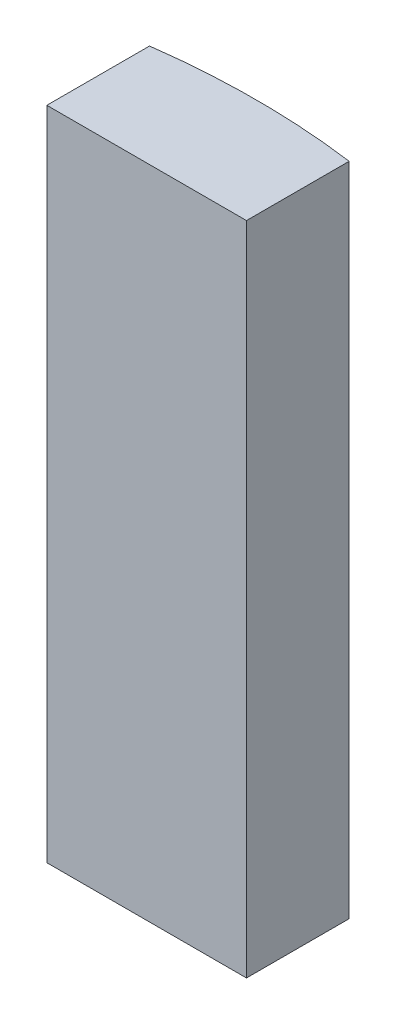
SolidWorks part; units mm, degrees
material "Acero inoxidable (ferrítico)"
ref_plane "Alzado" through (0, 0, 0) normal (0, 0, 1) x (1, 0, 0)
ref_plane "Planta" through (0, 0, 0) normal (0, 1, 0) x (1, 0, 0)
ref_plane "Vista lateral" through (0, 0, 0) normal (1, 0, 0) x (0, 0, -1)
sketch "Croquis1" plane through (0, 0, 0) normal (0, 1, 0) x (1, 0, 0)
  line L7 (0, 2) -> (0, 0.2)
  line L8 (0, 0.2) -> (3.5, 0.2)
  line L9 (3.5, 0.2) -> (3.5, 2)
  arc A0 (3.5, 2) -> (0, 2) centre (1.75, -10.8817) ccw
  dimension "D1" = 13
  dimension "D4" = 3.5
  dimension "D5" = 1.8
extrude "Saliente-Extruir1" add sketch "Croquis1" along normal blind 11.5
